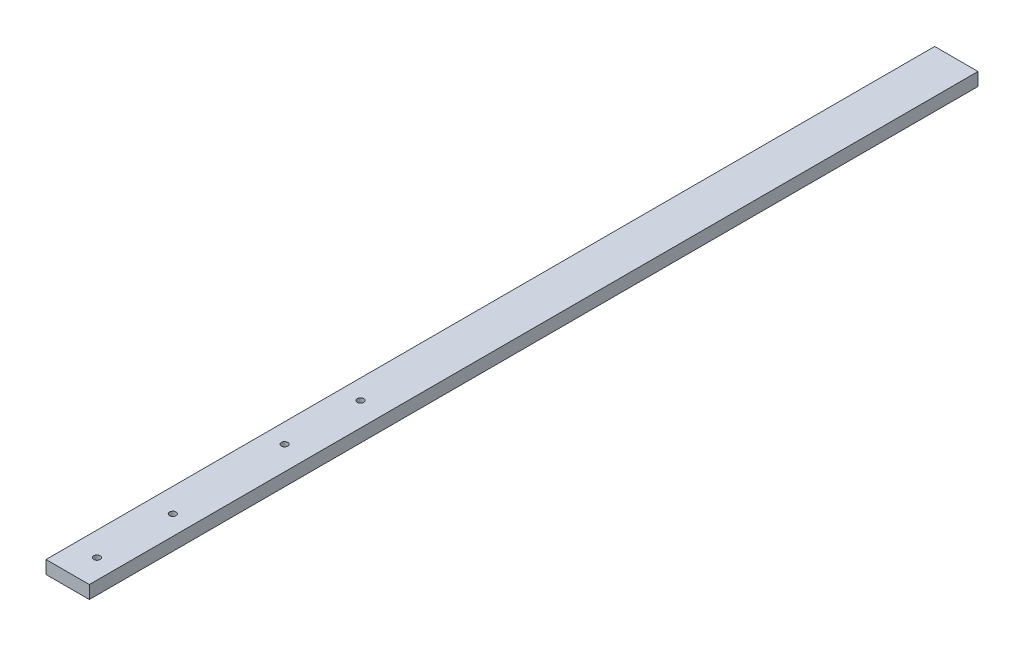
SolidWorks part; units mm, degrees
material "Pine"
ref_plane "Front Plane" through (0, 0, 0) normal (0, 0, 1) x (1, 0, 0)
ref_plane "Top Plane" through (0, 0, 0) normal (0, 1, 0) x (1, 0, 0)
ref_plane "Right Plane" through (0, 0, 0) normal (1, 0, 0) x (0, 0, -1)
sketch "Sketch1" plane through (0, 0, 0) normal (0, 1, 0) x (1, 0, 0)
  line L1 (10, -205) -> (-10, -205)
  line L2 (10, -205) -> (10, 205)
  line L3 (10, 205) -> (-10, 205)
  line L4 (-10, -205) -> (-10, 205)
  line L5 (10, -205) -> (-10, 205) construction
  line L6 (10, 205) -> (-10, -205) construction
  point P0 (0, 0)
  dimension "D1" = 20
  dimension "D2" = 410
extrude "Boss-Extrude1" add sketch "Sketch1" along normal blind 6
sketch "Sketch2" plane through (0, 6, 0) normal (0, 1, 0) x (1, 0, 0)
  line L0 (-10, -205) -> (10, -205) construction
  circle A0 centre (1, -192.5) radius 1.5
  circle A1 centre (1, -157.5) radius 1.5
  circle A2 centre (-1, -103.9) radius 1.5
  circle A3 centre (-1, -68.9) radius 1.5
  dimension "D1" = 3
  dimension "D3" = 3
  dimension "D8" = 3
  dimension "D9" = 3
  dimension "D2" = 1
  dimension "D4" = 35
  dimension "D5" = 12.5
  dimension "D6" = 53.6
  dimension "D7" = 35
  dimension "D10" = 2
extrude "Cut-Extrude1" cut sketch "Sketch2" against normal through all
